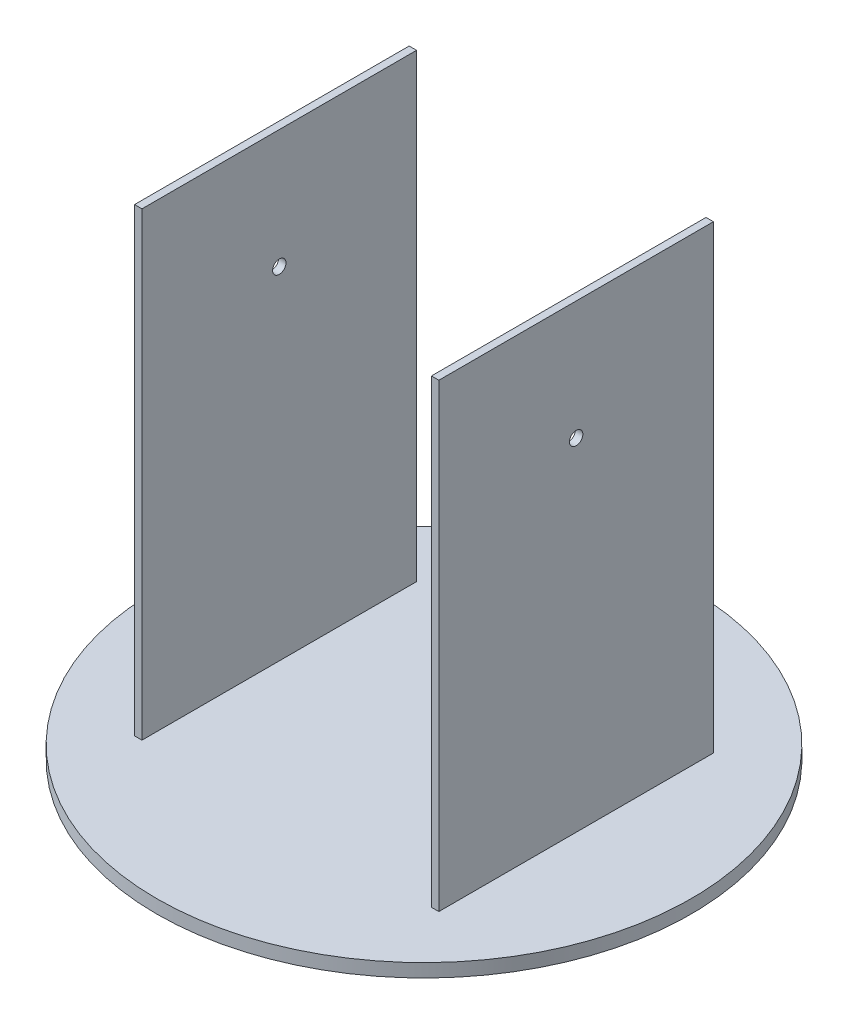
SolidWorks part; units mm, degrees
other "Markup1"
sketch "Sketch8" plane through (180, -9, -180) normal (0.9951, -0.0884, -0.0449) x (-0.0387, 0.0703, -0.9968)
ref_plane "Front Plane" through (0, 0, 0) normal (0, 0, 1) x (1, 0, 0)
ref_plane "Top Plane" through (0, 0, 0) normal (0, 1, 0) x (1, 0, 0)
ref_plane "Right Plane" through (0, 0, 0) normal (1, 0, 0) x (0, 0, -1)
sketch "Sketch2" plane through (0, 0, 0) normal (0, 1, 0) x (1, 0, 0)
  circle A0 centre (0, 0) radius 180
  dimension "D1" = 360
extrude "Boss-Extrude1" add sketch "Sketch2" against normal blind 9
sketch "Sketch3" plane through (0, 0, 0) normal (0, 1, 0) x (1, 0, 0)
  line L0 (-97.5, 92.5) -> (97.5, 92.5) construction
  line L9 (-102.5, -92.5) -> (-97.5, -92.5)
  line L10 (-102.5, -92.5) -> (-102.5, 92.5)
  line L11 (-102.5, 92.5) -> (-97.5, 92.5)
  line L12 (102.5, -92.5) -> (102.5, 92.5)
  line L13 (97.5, -92.5) -> (-97.5, -92.5) construction
  line L14 (0, -92.5) -> (0, 92.5) construction
  line L16 (97.5, 92.5) -> (97.5, -92.5)
  line L17 (-97.5, 92.5) -> (-97.5, -92.5)
  line L18 (97.5, 92.5) -> (102.5, 92.5)
  line L22 (97.5, -92.5) -> (102.5, -92.5)
  circle A1 centre (0, 0) radius 180 construction
  circle A2 centre (0, 0) radius 180
  point P0 (0, 0)
  dimension "D5" = 185
  dimension "D1" = 205
  dimension "D2" = 185
  dimension "D3" = 5
  dimension "D4" = 5
extrude "Boss-Extrude2" add sketch "Sketch3" along normal blind 310 contours L9 L17 L11 L10 | L18 L12 L22 L16
sketch "Sketch7" plane through (0, 0, 0) normal (1, 0, 0) x (0, 0, -1)
  line L0 (-92.5, 230) -> (92.5, 230) construction
  line L1 (-92.5, 310) -> (-92.5, 0) construction
  line L2 (92.5, 310) -> (92.5, 0) construction
  line L3 (-92.5, 310) -> (92.5, 310) construction
  circle A0 centre (0, 230) radius 4.5
  dimension "D2" = 9
  dimension "D1" = 80
extrude "Cut-Extrude2" cut sketch "Sketch7" against normal through all both and the other way through all contours A0
